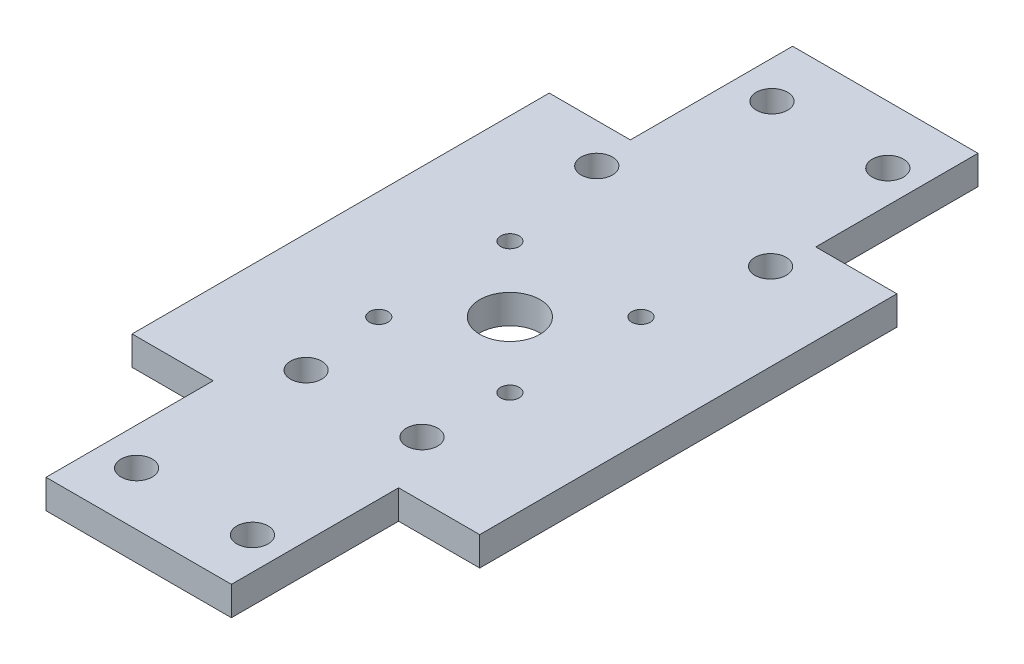
SolidWorks part; units mm, degrees
ref_plane "Front Plane" through (0, 0, 0) normal (0, 0, 1) x (1, 0, 0)
ref_plane "Top Plane" through (0, 0, 0) normal (0, 1, 0) x (1, 0, 0)
ref_plane "Right Plane" through (0, 0, 0) normal (1, 0, 0) x (0, 0, -1)
sketch "Sketch1" plane through (0, 0, 0) normal (0, 1, 0) x (1, 0, 0)
  line L1 (-19.05, -31.75) -> (19.05, -31.75)
  line L2 (-19.05, -31.75) -> (-19.05, 31.75)
  line L3 (-19.05, 31.75) -> (19.05, 31.75)
  line L4 (19.05, -31.75) -> (19.05, 31.75)
  line L5 (-19.05, -31.75) -> (19.05, 31.75) construction
  line L6 (-19.05, 31.75) -> (19.05, -31.75) construction
  point P0 (0, 0)
  dimension "D1" = 63.5
  dimension "D2" = 38.1
extrude "Boss-Extrude1" add sketch "Sketch1" along normal blind 3.175
sketch "Sketch2" plane through (0, 3.175, 0) normal (0, 1, 0) x (1, 0, 0)
  line L0 (-10.1459, 25.4) -> (13.8696, 25.4) construction
  line L2 (-10.1459, -25.654) -> (13.8696, -25.654) construction
  line L3 (-6.0718, 25.4) -> (-6.0718, -25.654) construction
  line L4 (6.6282, 25.4) -> (6.6282, -25.654) construction
  line L5 (19.05, 31.75) -> (-19.05, 31.75) construction
  line L6 (-19.05, -31.75) -> (19.05, -31.75) construction
  circle A0 centre (-6.0718, 25.4) radius 1.7145
  circle A1 centre (6.6282, 25.4) radius 1.7145
  circle A2 centre (6.6282, -25.654) radius 1.7145
  circle A3 centre (-6.0718, -25.654) radius 1.7145
  dimension "D3" = 12.7
  dimension "D5" = 24.0155
  dimension "D6" = 6.35
  dimension "D1" = 3.429
  dimension "D2" = 3.429
  dimension "D4" = 51.054
  dimension "D8" = 3.429
  dimension "D9" = 3.429
  dimension "D7" = 6.096
sketch "Sketch3" plane through (0, 3.175, 0) normal (0, 1, 0) x (1, 0, 0)
  line L0 (19.05, 0) -> (-19.05, 0) construction
  line L1 (19.05, -31.75) -> (19.05, 31.75) construction
  line L2 (-19.05, 31.75) -> (-19.05, -31.75) construction
  line L3 (0, 0) -> (0, -19.2588) construction
  line B0 (-8.0431, -1.3498) -> (7.7985, -17.1914) construction
  line B1 (-7.1304, -16.6047) -> (5.9731, -3.5011) construction
  circle B2 centre (0.0407, -9.4336) radius 3.302
  circle B3 centre (7.2249, -16.6178) radius 1.016
  circle B4 centre (-7.1435, -2.2494) radius 1.016
  circle B5 centre (-7.1435, -16.6178) radius 1.016
  circle B6 centre (7.2249, -2.2494) radius 1.016
sketch_block_instance "Block1-1"
sketch_block "Block1" parameters "D1"=6.604, "D2"=2.032, "D3"=2.032, "D4"=2.032, "D5"=2.032, "D6"=10.16, "D7"=10.16, "D8"=10.16, "D9"=10.16
extrude "holes for servo mount" cut sketch "Sketch3" against normal through all
extrude "holes for tilt servo bracket" cut sketch "Sketch2" against normal through all
sketch "Sketch4" plane through (0, 3.175, 0) normal (0, 1, 0) x (1, 0, 0)
  line L0 (-9.525, 9.652) -> (9.525, 9.652) construction
  line L1 (0, 9.652) -> (0, 17.2492) construction
  line L2 (0, 31.75) -> (0, 2.6211) construction
  line L3 (19.05, 31.75) -> (-19.05, 31.75) construction
  circle A0 centre (9.525, 9.652) radius 1.7145
  circle A1 centre (-9.525, 9.652) radius 1.7145
  dimension "D1" = 19.05
  dimension "D2" = 3.429
  dimension "D3" = 3.429
  dimension "D4" = 22.098
extrude "holes for pillow bracket" cut sketch "Sketch4" against normal through all
sketch "Sketch5" plane through (0, 3.175, 0) normal (0, 1, 0) x (1, 0, 0)
  line L0 (-10.16, 31.75) -> (-10.16, 13.97)
  line L1 (19.05, 31.75) -> (-19.05, 31.75) construction
  line L2 (-10.16, 13.97) -> (-19.05, 13.97)
  line L3 (-19.05, 31.75) -> (-19.05, -31.75) construction
  line L4 (-19.05, 13.97) -> (-19.05, 31.75)
  line L5 (-19.05, 31.75) -> (-10.16, 31.75)
  dimension "D1" = 17.78
  dimension "D2" = 8.89
extrude "Cut-Extrude1" cut sketch "Sketch5" against normal through all
mirror "Mirror1" about plane through (0, 0, 0) normal (1, 0, 0) of "Cut-Extrude1"
sketch "Sketch10" plane through (0, 3.175, 0) normal (0, 1, 0) x (1, 0, 0)
  line L0 (0, -31.75) -> (-10.16, -31.75)
  line L1 (-19.05, -31.75) -> (19.05, -31.75) construction
  line L2 (-10.16, -31.75) -> (-10.16, -50.0736)
  line L3 (-10.16, -50.0736) -> (10.16, -50.0736)
  line L4 (10.16, -50.0736) -> (10.16, -31.75)
  line L5 (10.16, -31.75) -> (0, -31.75)
  line L6 (-10.16, 16.8793) -> (-10.16, -60.081) construction
  line L7 (-10.16, 13.97) -> (-10.16, 31.75) construction
  line L8 (10.16, 16.8793) -> (10.16, -60.081) construction
  line L9 (10.16, 13.97) -> (10.16, 31.75) construction
  line L10 (-6.0718, 25.4) -> (-6.0718, -68.071) construction
  line L11 (6.6282, 25.4) -> (6.6282, -69.0876) construction
  line L12 (-6.0718, -44.2316) -> (6.6282, -44.2316) construction
  circle A0 centre (0.0407, -9.4336) radius 3.302 construction
  circle A1 centre (-6.0718, -44.2316) radius 1.7145
  circle A2 centre (6.6282, -44.2316) radius 1.7145
  dimension "D3" = 40.64
  dimension "D4" = 3.429
  dimension "D5" = 3.429
  dimension "D6" = 34.798
  dimension "D1" = 10.16
  dimension "D2" = 10.16
extrude "Boss-Extrude3" add sketch "Sketch10" against normal blind 3.175
